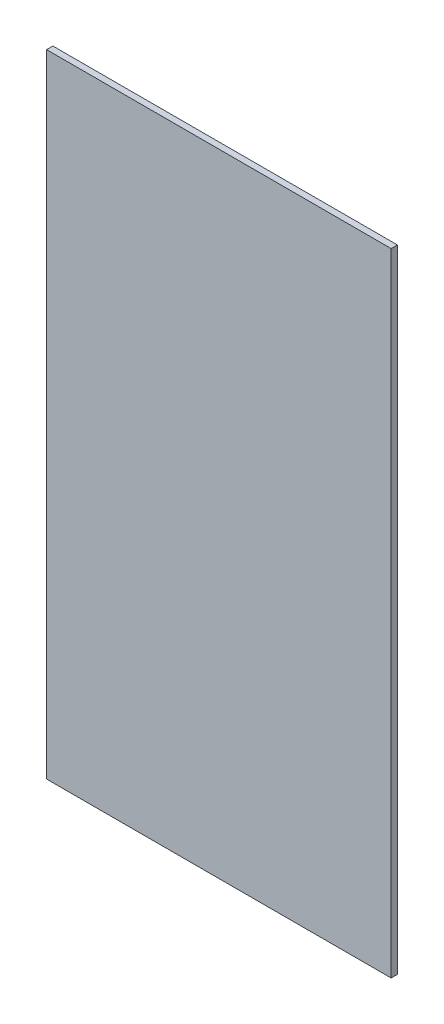
SolidWorks part; units mm, degrees
material "OSB_Plywood"
ref_plane "Front Plane" through (0, 0, 0) normal (0, 0, 1) x (1, 0, 0)
ref_plane "Top Plane" through (0, 0, 0) normal (0, 1, 0) x (1, 0, 0)
ref_plane "Right Plane" through (0, 0, 0) normal (1, 0, 0) x (0, 0, -1)
sketch "Sketch1" plane through (0, 0, 0) normal (0, 0, 1) x (1, 0, 0)
  line L1 (0, 0) -> (609.6, 0)
  line L2 (0, 0) -> (0, 1117.6)
  line L3 (0, 1117.6) -> (609.6, 1117.6)
  line L4 (609.6, 0) -> (609.6, 1117.6)
  dimension "D1" = 609.6
  dimension "D2" = 1117.6
extrude "Boss-Extrude1" add sketch "Sketch1" along normal blind 11.1125
